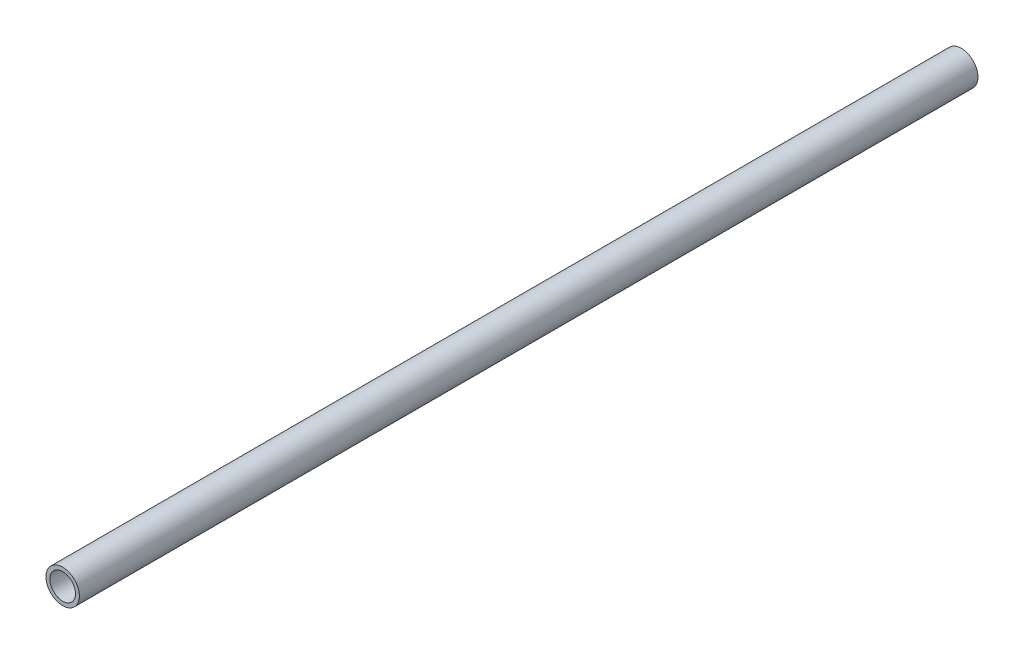
SolidWorks part; units mm, degrees
material "3.0255 (EN-AW 1350A)"
ref_plane "Alzado" through (0, 0, 0) normal (0, 0, 1) x (1, 0, 0)
ref_plane "Planta" through (0, 0, 0) normal (0, 1, 0) x (1, 0, 0)
ref_plane "Vista lateral" through (0, 0, 0) normal (1, 0, 0) x (0, 0, -1)
sketch "Croquis1" plane through (0, 0, 0) normal (0, 0, 1) x (1, 0, 0)
  circle A0 centre (0, 0) radius 5
  circle A1 centre (0, 0) radius 6.5
  dimension "D1" = 13
  dimension "D2" = 1.5
extrude "Saliente-Extruir1" add sketch "Croquis1" along normal mid plane 350
